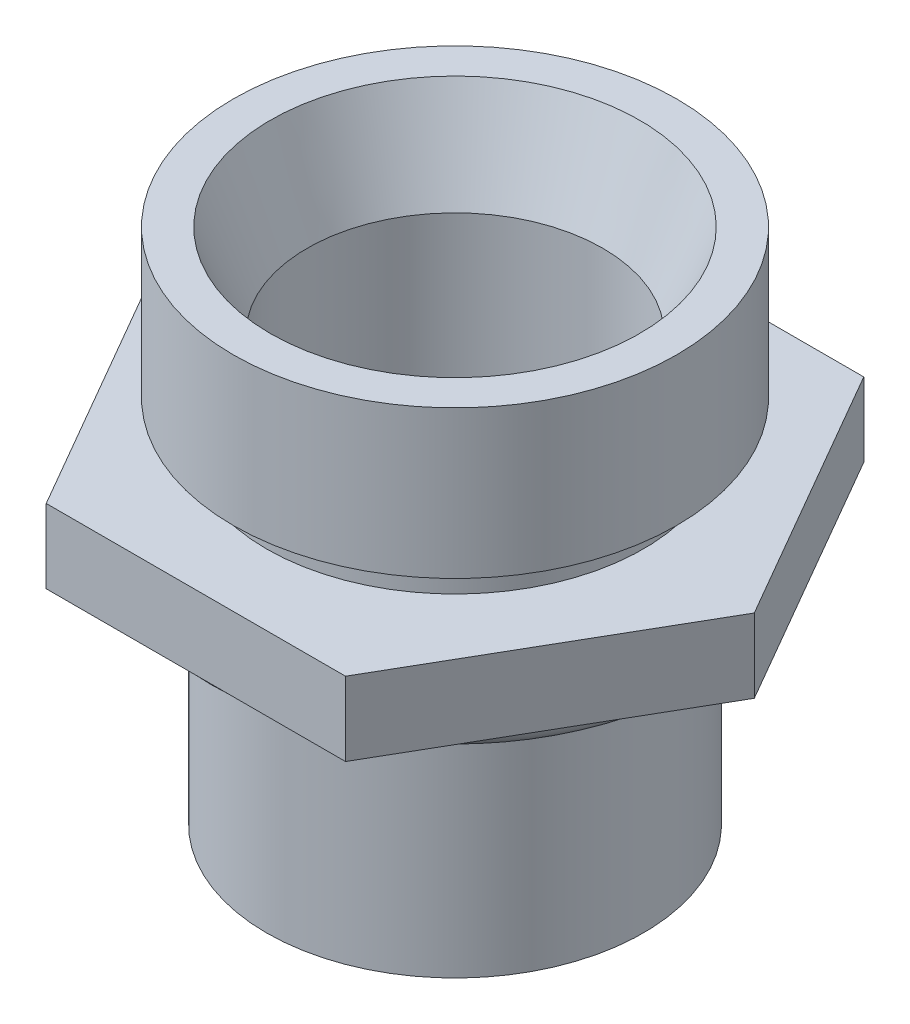
SolidWorks part; units mm, degrees
ref_plane "Спереди (Плоскость XY)" through (0, 0, 0) normal (0, 0, 1) x (1, 0, 0)
ref_plane "Сверху (Плоскость XZ)" through (0, 0, 0) normal (0, 1, 0) x (1, 0, 0)
ref_plane "Справа (Плоскость ZY)" through (0, 0, 0) normal (1, 0, 0) x (0, 0, -1)
sketch "Эскиз1" plane through (0, 0, 0) normal (0, 0, 1) x (1, 0, 0)
  line L0 (0, 12.4404) -> (0, -10.0465) construction
  line L1 (-5.1, 3.4375) -> (-8.1, 3.4375)
  line L2 (-4, -5.5625) -> (-4, 5.9375)
  line L3 (-5.1, 3.4375) -> (-5.1, 4.4375)
  line L4 (-5.1, 4.4375) -> (-6, 4.4375)
  line L5 (-6, 4.4375) -> (-6, 8.4375)
  line L6 (-6, 8.4375) -> (-5, 8.4375)
  line L7 (-8.1, 3.4375) -> (-8.1, 1.4375)
  line L8 (-8.1, 1.4375) -> (-6.9, 1.4375)
  line L9 (-5.1, -5.5625) -> (-5.1, 1.4375)
  line L10 (-6.9, 1.4375) -> (-6.9, 2.4375)
  line L11 (-6.9, 2.4375) -> (-5.1, 2.4375)
  line L12 (-5.1, 2.4375) -> (-5.1, 1.4375)
  line L13 (-5.1, -5.5625) -> (-4, -5.5625)
  line L15 (-4, 5.9375) -> (-5, 8.4375)
  circle A0 centre (-6, 1.5375) radius 0.8
  point P17 (-6, 2.3375)
  point P19 (-5.2, 1.5375)
  dimension "D10" = 0.1
  dimension "D4" = 1.6
  dimension "D2" = 6
  dimension "D3" = 1
  dimension "D5" = 4
  dimension "D6" = 2
  dimension "D7" = 1.8
  dimension "D8" = 7
  dimension "D9" = 1
  dimension "D11" = 0.1
  dimension "D12" = 4
  dimension "D13" = 2.5
revolve "Повернуть1" add sketch "Эскиз1" angle 360 about L0
sketch "Эскиз3" plane through (0, 3.4375, 0) normal (0, 1, 0) x (1, 0, 0)
  line L0 (-8.1, 0) -> (-4.0504, 7.0134)
  line L1 (-4.0504, 7.0134) -> (4.0486, 7.0144)
  line L2 (4.0486, 7.0144) -> (8.1, 0)
  line L3 (8.1, 0) -> (4.0504, -7.0134)
  line L4 (4.0504, -7.0134) -> (-4.0486, -7.0144)
  line L5 (-4.0486, -7.0144) -> (-8.1, 0)
  circle A3 centre (0.002, 0) radius 12.6424
  point P6 (-4.0504, 7.0134)
  point P9 (8.101, 0.001)
  point P15 (-8.099, -0.001)
  point P18 (0.001, 0)
  point P19 (4.0486, 7.0144)
  point P20 (8.099, 0.001)
  point P21 (4.0504, -7.0134)
  point P22 (-4.0486, -7.0144)
  point P23 (0, 0)
  dimension "D1" = 6
extrude "Вырез-Вытянуть2" cut sketch "Эскиз3" against normal blind 10
